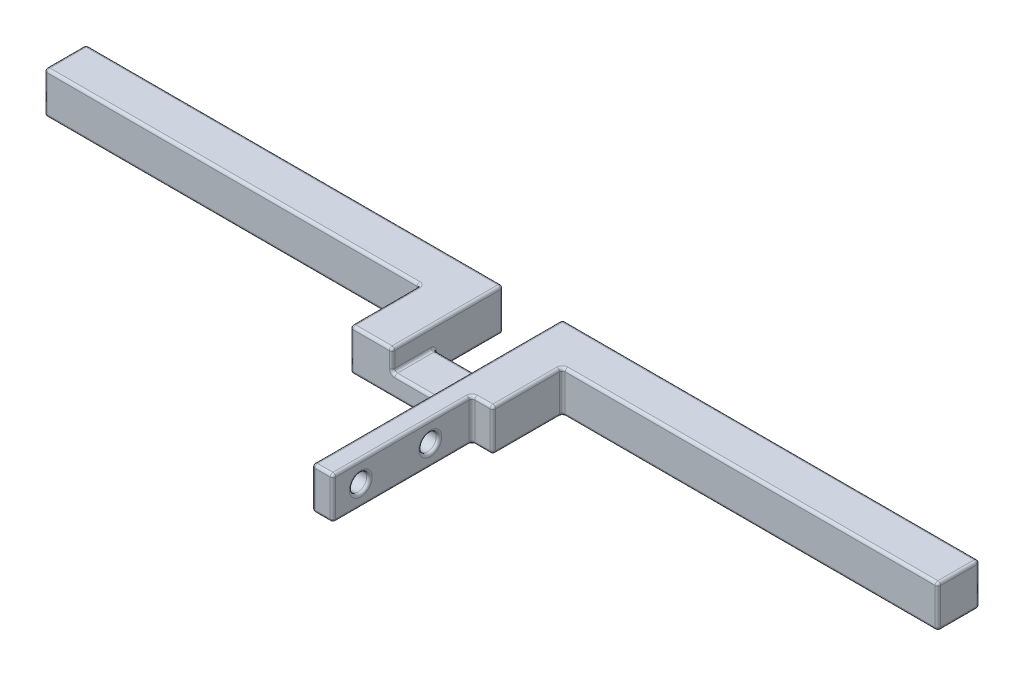
SolidWorks part; units mm, degrees
ref_plane "前视基准面" through (0, 0, 0) normal (0, 0, 1) x (1, 0, 0)
ref_plane "上视基准面" through (0, 0, 0) normal (0, 1, 0) x (1, 0, 0)
ref_plane "右视基准面" through (0, 0, 0) normal (1, 0, 0) x (0, 0, -1)
other "Configuration Table"
sketch "草图1" plane through (0, 0, 0) normal (0, 1, 0) x (1, 0, 0)
  line L6 (4.25, 0) -> (-4.25, 0)
  line L8 (4.25, 0) -> (4.25, 10)
  line L9 (4.25, 10) -> (64.25, 10)
  line L10 (64.25, 10) -> (64.25, 4)
  line L11 (64.25, 4) -> (10.25, 4)
  line L13 (-4.25, 0) -> (-4.25, 10)
  line L14 (-4.25, 10) -> (-64.25, 10)
  line L15 (-64.25, 10) -> (-64.25, 4)
  line L16 (-64.25, 4) -> (-10.25, 4)
  line L17 (-10.25, 4) -> (-10.25, -6)
  line L18 (-10.25, -6) -> (4.25, -6)
  line L19 (4.25, -6) -> (4.25, -26)
  line L20 (4.25, -26) -> (7.25, -26)
  line L21 (10.25, 4) -> (10.25, -6)
  line L22 (10.25, -6) -> (7.25, -6)
  line L23 (7.25, -6) -> (7.25, -26)
  line L24 (0, 0) -> (0, 20.5311) construction
  point P0 (0, 0)
  dimension "D1" = 8.5
  dimension "D2" = 6
  dimension "D3" = 10
  dimension "D4" = 6
  dimension "D5" = 3
  dimension "D6" = 20
  dimension "D7" = 6
  dimension "D8" = 60
extrude "凸台-拉伸1" add sketch "草图1" along normal blind 6 contours L23 L20 L19 L18 L17 L16 L15 L14 L13 L6 L8 L9 L10 L11 L21 L22
sketch "草图2" plane through (0, 6, 0) normal (0, 1, 0) x (1, 0, 0)
  line L1 (4.25, 0) -> (-4.25, 0)
  line L2 (4.25, 0) -> (4.25, -6)
  line L3 (4.25, -6) -> (-4.25, -6)
  line L4 (-4.25, 0) -> (-4.25, -6)
  line L6 (-10.25, -6) -> (4.25, -6) construction
  point P5 (-4.25, 0)
  point P6 (-4.25, -6)
  point P7 (-3, 0)
  point P8 (-3, 0)
extrude "切除-拉伸1" cut sketch "草图2" against normal blind 3
sketch "草图3" plane through (7.25, 0, 0) normal (1, 0, 0) x (0, 0, -1)
  line L0 (-12, 0) -> (-12, 6) construction
  line L1 (-6, 0) -> (-26, 0) construction
  line L2 (-6, 6) -> (-26, 6) construction
  line L3 (-6, 6) -> (-6, 0) construction
  line L4 (-22, 3) -> (-12, 3) construction
  circle A0 centre (-12, 3) radius 1.25
  circle A1 centre (-22, 3) radius 1.25
  point P4 (-12, 3)
  dimension "D2" = 2.5
  dimension "D1" = 6
  dimension "D3" = 10
extrude "切除-拉伸2" cut sketch "草图3" against normal through all
fillet "圆角1" radius 0.4 55 edges at (10.25, 3, 6) (10.25, 3, -4) (7.25, 3, 26) (7.25, 3, 6) (7.25, 3, 10.75) (4.25, 3, -10) (4.25, 3, 26) (4.25, 1.5, 6) (4.25, 1.5, 0) (4.25, 3, 13.25) (-4.25, 1.5, 0) (-4.25, 4.5, 6) (-4.25, 3, -10) (64.25, 3, -4) (64.25, 3, -10) (-64.25, 3, -10) (-64.25, 3, -4) (-10.25, 3, -4) (-10.25, 3, 6) (0, 3, 6) (-4.25, 3, 3) (0, 3, 0) (4.25, 3, 3) (-10.25, 6, 1) (-37.25, 6, -4) (-64.25, 6, -7) (-34.25, 6, -10) (-4.25, 6, -2) (-7.25, 6, 6) (64.25, 6, -7) (37.25, 6, -4) (10.25, 6, 1) (8.75, 6, 6) (7.25, 6, 16) (5.75, 6, 26) (4.25, 6, 8) (34.25, 6, -10) (10.25, 0, 1) (37.25, 0, -4) (64.25, 0, -7) (34.25, 0, -10) (4.25, 0, -5) (0, 0, 0) (-4.25, 0, -5) (-34.25, 0, -10) (-64.25, 0, -7) (-37.25, 0, -4) (-10.25, 0, 1) (-3, 0, 6) (4.25, 0, 16) (5.75, 0, 26) (7.25, 0, 16) (8.75, 0, 6) (7.25, 3, 20.75) (4.25, 3, 23.25)
